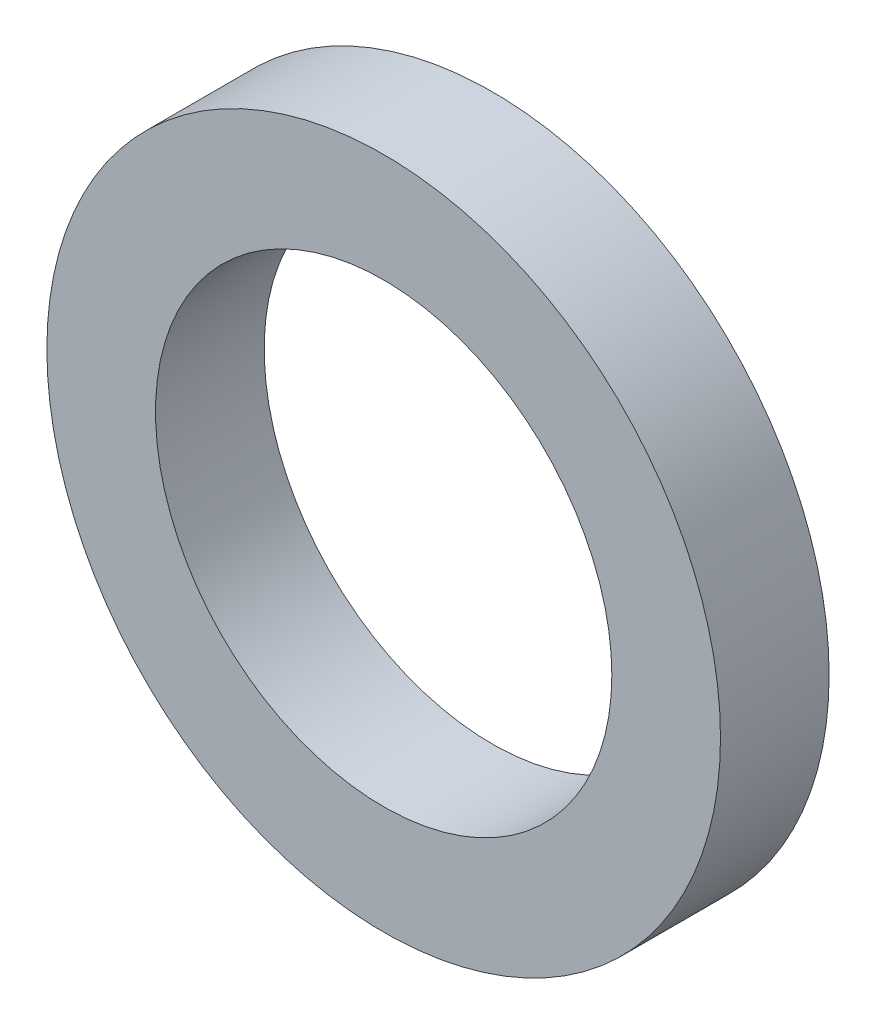
SolidWorks part; units mm, degrees
ref_plane "Front Plane" through (0, 0, 0) normal (0, 0, 1) x (1, 0, 0)
ref_plane "Top Plane" through (0, 0, 0) normal (0, 1, 0) x (1, 0, 0)
ref_plane "Right Plane" through (0, 0, 0) normal (1, 0, 0) x (0, 0, -1)
sketch "Sketch1" plane through (0, 0, 0) normal (0, 0, 1) x (1, 0, 0)
  circle A1 centre (0, 0) radius 3.1
  circle A2 centre (0, 0) radius 2.1
  dimension "D1" = 6.2
extrude "Boss-Extrude1" add sketch "Sketch1" along normal blind 1
equation "\"ID\"= 4.2"
equation "\"D2@Sketch1\"=\"ID\""
